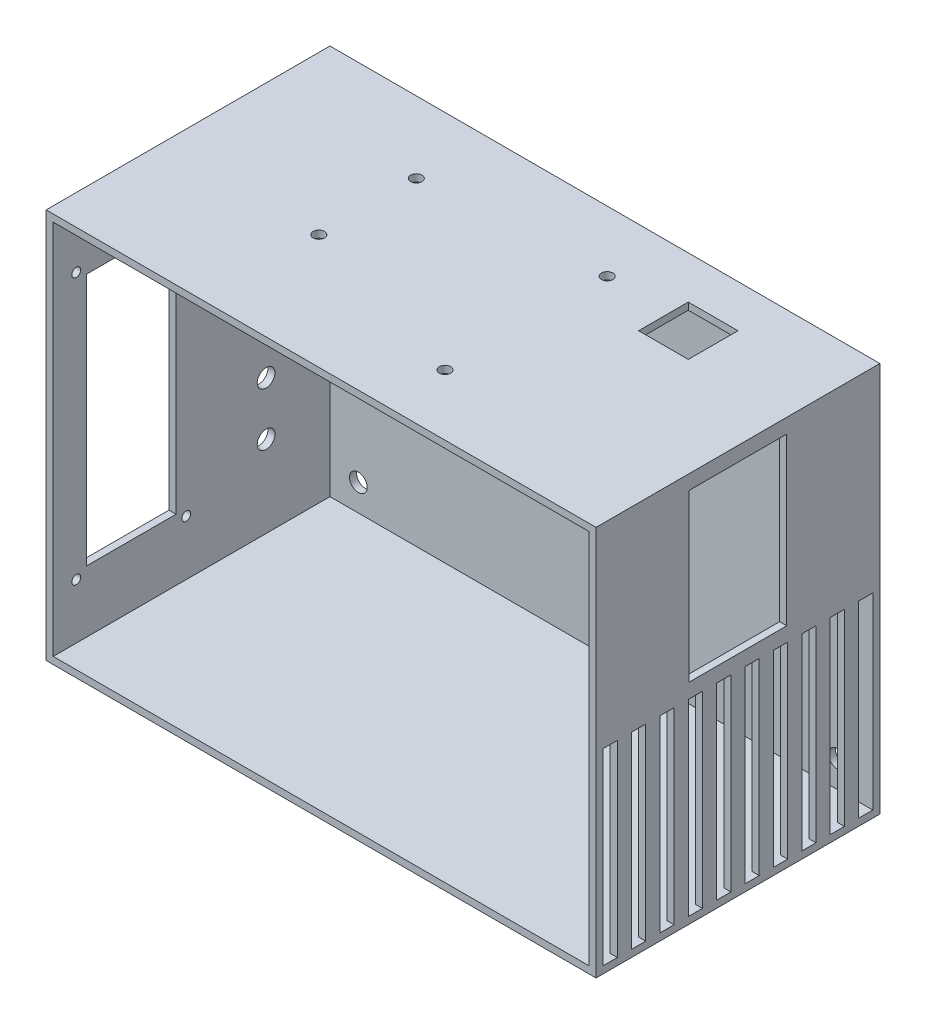
SolidWorks part; units mm, degrees
ref_plane "Front Plane" through (0, 0, 0) normal (0, 0, 1) x (1, 0, 0)
ref_plane "Top Plane" through (0, 0, 0) normal (0, 1, 0) x (1, 0, 0)
ref_plane "Right Plane" through (0, 0, 0) normal (1, 0, 0) x (0, 0, -1)
sketch "Sketch1" plane through (0, 0, 0) normal (0, 0, 1) x (1, 0, 0)
  line L1 (0, 0) -> (155, 0)
  line L2 (0, 0) -> (0, 110)
  line L3 (0, 110) -> (155, 110)
  line L4 (155, 0) -> (155, 110)
  dimension "D1" = 155
  dimension "D2" = 110
extrude "Boss-Extrude1" add sketch "Sketch1" along normal blind 80 contours L2 L1 L4 L3
sketch "Sketch2" plane through (0, 0, 80) normal (0, 0, 1) x (1, 0, 0)
  line L0 (0, 110) -> (2, 110) construction
  line L1 (0, 110) -> (155, 110) construction
  line L2 (0, 110) -> (0, 108) construction
  line L3 (0, 0) -> (0, 110) construction
  line L4 (155, 0) -> (155, 2) construction
  line L5 (155, 0) -> (155, 110) construction
  line L6 (155, 0) -> (153, 0) construction
  line L7 (0, 0) -> (155, 0) construction
  line L8 (0, 108) -> (2, 108) construction
  line L9 (2, 108) -> (2, 110) construction
  line L10 (155, 2) -> (153, 2) construction
  line L11 (153, 2) -> (153, 0) construction
  line L13 (153, 2) -> (2, 2)
  line L14 (153, 2) -> (153, 108)
  line L15 (153, 108) -> (2, 108)
  line L16 (2, 2) -> (2, 108)
  dimension "D1" = 2
  dimension "D2" = 2
  dimension "D3" = 2
  dimension "D4" = 2
extrude "Cut-Extrude1" cut sketch "Sketch2" against normal blind 78 contours L14 L13 L16 L15
sketch "Sketch3" plane through (0, 0, 2) normal (0, 0, 1) x (1, 0, 0)
  line L0 (2, 2) -> (6, 2) construction
  line L1 (153, 2) -> (2, 2) construction
  line L2 (153, 2) -> (149, 2) construction
  line L3 (2, 108) -> (6, 108) construction
  line L4 (153, 108) -> (2, 108) construction
  line L5 (2, 108) -> (2, 104.5) construction
  line L6 (2, 2) -> (2, 108) construction
  line L7 (149, 2) -> (149, 5.5) construction
  line L8 (2, 104.5) -> (6, 104.5) construction
  line L9 (6, 104.5) -> (6, 108) construction
  line L10 (6, 5.5) -> (10, 5.5) construction
  line L11 (6, 104.5) -> (149, 104.5)
  line L12 (6, 104.5) -> (6, 5.5)
  line L13 (6, 5.5) -> (149, 5.5)
  line L14 (149, 104.5) -> (149, 5.5)
  line L15 (10, 5.5) -> (10, 9.5) construction
  line L16 (149, 104.5) -> (145, 104.5) construction
  line L17 (145, 104.5) -> (145, 100.5) construction
  line L19 (10, 9.5) -> (145, 9.5)
  line L20 (10, 9.5) -> (10, 100.5)
  line L21 (10, 100.5) -> (145, 100.5)
  line L22 (145, 9.5) -> (145, 100.5)
  circle A0 centre (145, 100.5) radius 2.5
  circle A1 centre (145, 9.5) radius 2.5
  circle A2 centre (10, 9.5) radius 2.5
  circle A3 centre (10, 100.5) radius 2.5
  dimension "D10" = 5
  dimension "D11" = 5
  dimension "D12" = 5
  dimension "D13" = 5
  dimension "D1" = 4
  dimension "D2" = 3.5
  dimension "D3" = 4
  dimension "D4" = 4
  dimension "D5" = 3.5
  dimension "D6" = 4
  dimension "D7" = 4
  dimension "D8" = 4
  dimension "D9" = 4
extrude "Cut-Extrude2" cut sketch "Sketch3" against normal blind 2 contours A3 | A0 | A2 | A1
sketch "Sketch4" plane through (155, 0, 0) normal (1, 0, 0) x (0, 0, -1)
  line L1 (-53.75, 59.1) -> (-26.25, 59.1)
  line L3 (0, 55) -> (-80, 55) construction
  line L4 (0, 0) -> (0, 110) construction
  line L5 (-80, 0) -> (-80, 110) construction
  line L7 (-26.25, 105.9) -> (-26.25, 59.1)
  line L14 (-53.75, 105.9) -> (-26.25, 105.9)
  line L15 (-53.75, 105.9) -> (-53.75, 59.1)
  dimension "D1" = 46.8
  dimension "D2" = 27.5
sketch "Sketch7" plane through (0, 110, 0) normal (0, 1, 0) x (1, 0, 0)
  line L0 (0, -40) -> (155, -40) construction
  line L1 (0, -80) -> (0, 0) construction
  line L2 (155, -80) -> (155, 0) construction
  line L3 (77.5, 0) -> (77.5, -80) construction
  line L4 (0, 0) -> (155, 0) construction
  line L5 (0, -80) -> (155, -80) construction
  line L6 (110.52, -65.4) -> (95.28, -65.4) construction
  line L7 (44.48, -65.4) -> (110.52, -65.4)
  line L8 (44.48, -65.4) -> (44.48, -14.6)
  line L9 (44.48, -14.6) -> (110.52, -14.6)
  line L10 (110.52, -65.4) -> (110.52, -14.6)
  line L11 (44.48, -65.4) -> (110.52, -14.6) construction
  line L12 (44.48, -14.6) -> (110.52, -65.4) construction
  line L13 (95.28, -65.4) -> (95.28, -62.86) construction
  line L14 (110.52, -14.6) -> (95.28, -14.6) construction
  line L15 (44.48, -14.6) -> (44.48, -20.1445) construction
  line L16 (44.48, -65.4) -> (44.48, -47.62) construction
  line L17 (95.28, -14.6) -> (95.28, -17.14) construction
  line L18 (44.48, -65.4) -> (44.48, -19.68) construction
  circle A0 centre (44.48, -20.1445) radius 1.6
  circle A1 centre (95.28, -17.14) radius 1.6
  circle A2 centre (95.28, -62.86) radius 1.6
  circle A3 centre (44.48, -47.62) radius 1.6
  point P12 (77.5, -40)
  dimension "D9" = 3.2
  dimension "D10" = 3.2
  dimension "D11" = 3.2
  dimension "D12" = 3.2
  dimension "D1" = 66.04
  dimension "D2" = 50.8
  dimension "D3" = 15.24
  dimension "D4" = 2.54
  dimension "D5" = 15.24
  dimension "D6" = 2.54
  dimension "D7" = 17.78
  dimension "D8" = 45.72
extrude "Cut-Extrude7" cut sketch "Sketch7" against normal blind 2 contours A0 | A1 | A3 | A2
extrude "Cut-Extrude8" cut sketch "Sketch4" against normal blind 2
sketch "Sketch8" plane through (155, 0, 0) normal (1, 0, 0) x (0, 0, -1)
  line L0 (-80, 55) -> (0, 55) construction
  line L1 (-80, 0) -> (-80, 110) construction
  line L2 (0, 0) -> (0, 110) construction
  line L3 (0, 0) -> (-2, 0) construction
  line L4 (-80, 0) -> (0, 0) construction
  line L5 (-2, 0) -> (-2, 2) construction
  line L6 (-80, 0) -> (-78, 0) construction
  line L7 (-78, 0) -> (-78, 2) construction
  line L8 (-70, 2) -> (-70, 55)
  line L9 (-78, 2) -> (-74, 2)
  line L10 (-78, 2) -> (-78, 55)
  line L11 (-78, 55) -> (-74, 55)
  line L12 (-74, 2) -> (-74, 55)
  line L13 (-70, 2) -> (-66, 2)
  line L14 (-66, 2) -> (-66, 55)
  line L15 (-70, 55) -> (-66, 55)
  line L16 (-62, 2) -> (-62, 55)
  line L17 (-62, 2) -> (-58, 2)
  line L18 (-58, 2) -> (-58, 55)
  line L19 (-62, 55) -> (-58, 55)
  line L20 (-54, 2) -> (-54, 55)
  line L21 (-54, 2) -> (-50, 2)
  line L22 (-50, 2) -> (-50, 55)
  line L23 (-54, 55) -> (-50, 55)
  line L24 (-46, 2) -> (-46, 55)
  line L25 (-46, 2) -> (-42, 2)
  line L26 (-42, 2) -> (-42, 55)
  line L27 (-46, 55) -> (-42, 55)
  line L28 (-38, 2) -> (-38, 55)
  line L29 (-38, 2) -> (-34, 2)
  line L30 (-34, 2) -> (-34, 55)
  line L31 (-38, 55) -> (-34, 55)
  line L32 (-30, 2) -> (-30, 55)
  line L33 (-30, 2) -> (-26, 2)
  line L34 (-26, 2) -> (-26, 55)
  line L35 (-30, 55) -> (-26, 55)
  line L36 (-22, 2) -> (-22, 55)
  line L37 (-22, 2) -> (-18, 2)
  line L38 (-18, 2) -> (-18, 55)
  line L39 (-22, 55) -> (-18, 55)
  line L40 (-14, 2) -> (-14, 55)
  line L41 (-14, 2) -> (-10, 2)
  line L42 (-10, 2) -> (-10, 55)
  line L43 (-14, 55) -> (-10, 55)
  line L44 (-6, 2) -> (-6, 55)
  line L45 (-6, 2) -> (-2, 2)
  line L46 (-2, 2) -> (-2, 55)
  line L47 (-6, 55) -> (-2, 55)
  dimension "D1" = 2
  dimension "D2" = 2
  dimension "D3" = 2
  dimension "D4" = 2
  dimension "D5" = 4
extrude "Cut-Extrude9" cut sketch "Sketch8" against normal blind 2
sketch "Sketch9" plane through (0, 110, 0) normal (0, 1, 0) x (1, 0, 0)
  line L0 (0, -40) -> (155, -40) construction
  line L1 (0, -80) -> (0, 0) construction
  line L2 (155, -80) -> (155, 0) construction
  line L3 (155, -40) -> (120, -40) construction
  line L4 (120, -40) -> (120, -26) construction
  line L5 (120, -26) -> (113, -26) construction
  line L7 (113, -26) -> (127, -26)
  line L8 (113, -26) -> (113, -12)
  line L9 (113, -12) -> (127, -12)
  line L10 (127, -26) -> (127, -12)
  dimension "D1" = 35
  dimension "D2" = 14
  dimension "D3" = 7
  dimension "D4" = 14
  dimension "D5" = 14
extrude "Cut-Extrude10" cut sketch "Sketch9" against normal blind 2
sketch "Sketch10" plane through (0, 0, 0) normal (-1, 0, 0) x (0, 0, 1)
  line L0 (40, 110) -> (40, 0) construction
  line L1 (80, 110) -> (0, 110) construction
  line L2 (80, 0) -> (0, 0) construction
  line L3 (80, 55) -> (0, 55) construction
  line L4 (80, 0) -> (80, 110) construction
  line L5 (0, 0) -> (0, 110) construction
  line L6 (40, 55) -> (80, 55) construction
  line L7 (80, 55) -> (60, 55) construction
  line L8 (60, 55) -> (58, 55) construction
  line L9 (40, 95) -> (42.5, 95) construction
  line L10 (40, 15) -> (76, 15)
  line L11 (40, 15) -> (40, 95)
  line L12 (40, 95) -> (76, 95)
  line L13 (76, 15) -> (76, 95)
  line L14 (40, 15) -> (76, 95) construction
  line L15 (40, 95) -> (76, 15) construction
  line L16 (42.5, 95) -> (42.5, 92.5) construction
  line L17 (76, 15) -> (73.5, 15) construction
  line L18 (73.5, 15) -> (73.5, 17.5) construction
  line L19 (76, 15) -> (76, 19.4) construction
  line L20 (42.5, 92.5) -> (73.5, 92.5)
  line L21 (42.5, 92.5) -> (42.5, 17.5)
  line L22 (42.5, 17.5) -> (73.5, 17.5)
  line L23 (73.5, 92.5) -> (73.5, 17.5)
  line L24 (76, 19.4) -> (70.6, 19.4) construction
  line L25 (40, 95) -> (45.4, 95) construction
  line L26 (45.4, 95) -> (45.4, 90.6) construction
  line L28 (45.4, 90.6) -> (70.6, 90.6)
  line L29 (45.4, 90.6) -> (45.4, 19.4)
  line L30 (45.4, 19.4) -> (70.6, 19.4)
  line L31 (70.6, 90.6) -> (70.6, 19.4)
  circle A0 centre (73.5, 92.5) radius 1.25
  circle A1 centre (73.5, 17.5) radius 1.25
  circle A2 centre (42.5, 17.5) radius 1.25
  circle A3 centre (42.5, 92.5) radius 1.25
  dimension "D8" = 2.5
  dimension "D9" = 2.5
  dimension "D10" = 2.5
  dimension "D11" = 2.5
  dimension "D1" = 2
  dimension "D2" = 80
  dimension "D3" = 36
  dimension "D4" = 2.5
  dimension "D5" = 2.5
  dimension "D6" = 2.5
  dimension "D7" = 2.5
  dimension "D12" = 4.4
  dimension "D13" = 5.4
  dimension "D14" = 4.4
  dimension "D15" = 5.4
extrude "Cut-Extrude12" cut sketch "Sketch10" against normal blind 2 contours L31 L28 L29 L30 | A3 | A0 | A2 | A1
sketch "Sketch11" plane through (0, 0, 0) normal (-1, 0, 0) x (0, 0, 1)
  line L0 (40, 110) -> (40, 0) construction
  line L1 (80, 110) -> (0, 110) construction
  line L2 (80, 0) -> (0, 0) construction
  line L3 (20, 110) -> (20, 0) construction
  line L4 (0, 55) -> (0, 110) construction
  line L5 (0, 0) -> (0, 110) construction
  line L6 (40, 55) -> (0, 55) construction
  line L7 (0, 82.5) -> (40, 82.5) construction
  circle A0 centre (20, 55) radius 2.5
  circle A1 centre (20, 40) radius 2.5
  circle A2 centre (20, 25) radius 2.5
  circle A3 centre (20, 82.5) radius 4.5
  dimension "D1" = 5
  dimension "D3" = 9
  dimension "D2" = 3
extrude "Cut-Extrude13" cut sketch "Sketch11" against normal blind 2
